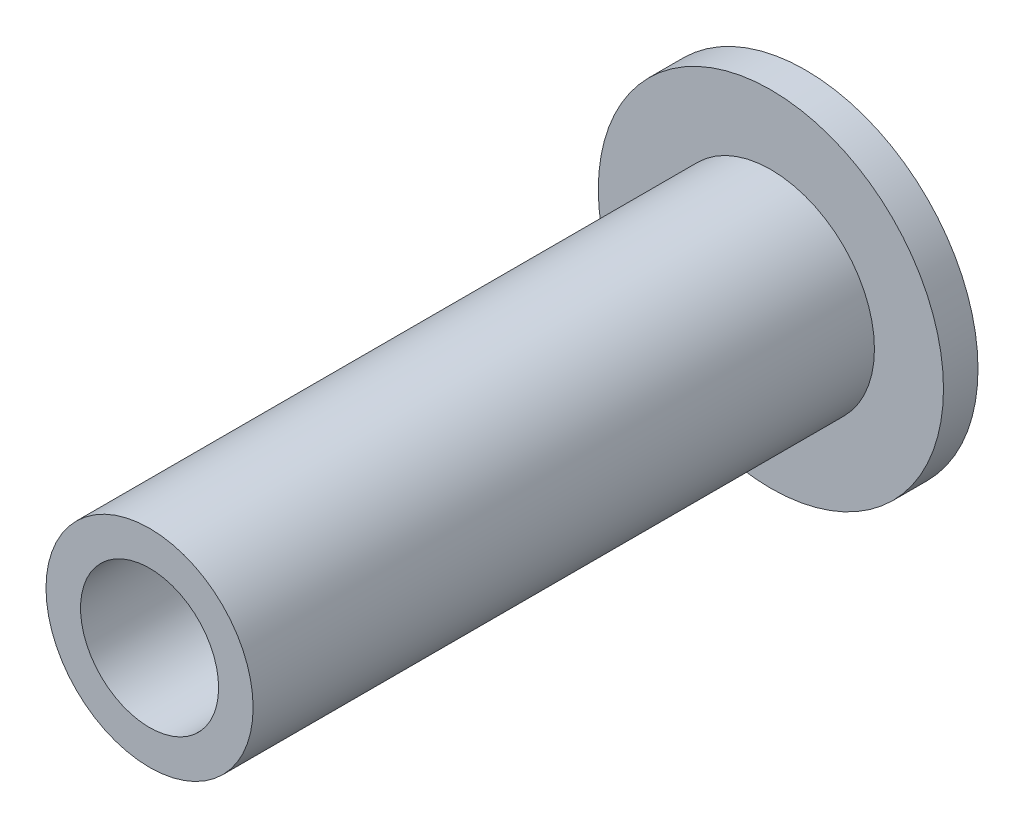
SolidWorks part; units mm, degrees
material "AISI 1020 Acier laminé à froid"
ref_plane "Plan de face" through (0, 0, 0) normal (0, 0, 1) x (1, 0, 0)
ref_plane "Plan de dessus" through (0, 0, 0) normal (0, 1, 0) x (1, 0, 0)
ref_plane "Plan de droite" through (0, 0, 0) normal (1, 0, 0) x (0, 0, -1)
sketch "Esquisse1" plane through (0, 0, 0) normal (1, 0, 0) x (0, 0, -1)
  line L0 (-27.6552, 0) -> (2.4828, 0) construction
  line L1 (-18, 3) -> (0, 3)
  line L2 (0, 3) -> (0, 5)
  line L3 (0, 5) -> (1, 5)
  line L4 (-18, 3) -> (-18, 2)
  line L5 (-18, 2) -> (-1.1547, 2)
  line L6 (-1.1547, 2) -> (0, 0)
  line L7 (1.4764, 0) -> (0, 0)
  arc A1 (1.4764, 0) -> (1, 5) centre (-25, 0) ccw
  dimension "D4" = 1
  dimension "D1" = 3
  dimension "D2" = 60
  dimension "D3" = 4
  dimension "D5" = 18
  dimension "D6" = 5
revolve "Révolution1" add sketch "Esquisse1" angle 360 about L0
